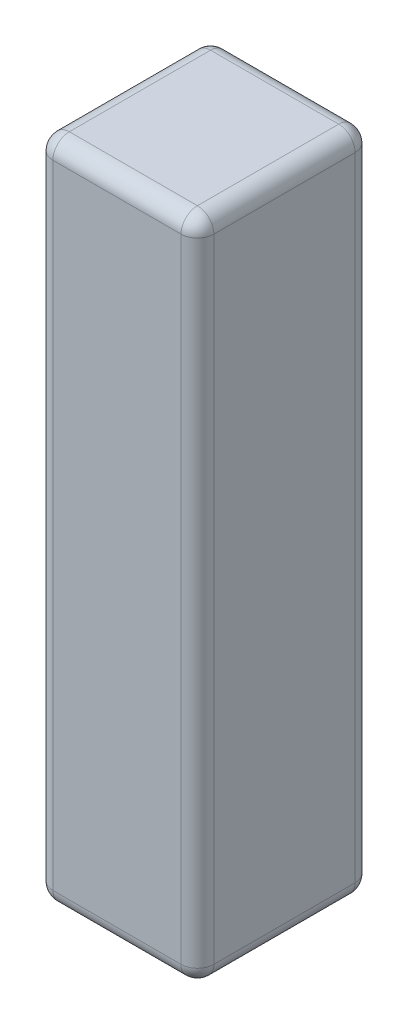
SolidWorks part; units mm, degrees
ref_plane "Front Plane" through (0, 0, 0) normal (0, 0, 1) x (1, 0, 0)
ref_plane "Top Plane" through (0, 0, 0) normal (0, 1, 0) x (1, 0, 0)
ref_plane "Right Plane" through (0, 0, 0) normal (1, 0, 0) x (0, 0, -1)
sketch "Sketch1" plane through (0, 0, 0) normal (0, 1, 0) x (1, 0, 0)
  line L1 (12.446, 13.462) -> (-12.446, 13.462)
  line L2 (12.446, 13.462) -> (12.446, -13.462)
  line L3 (12.446, -13.462) -> (-12.446, -13.462)
  line L4 (-12.446, 13.462) -> (-12.446, -13.462)
  line L5 (12.446, 13.462) -> (-12.446, -13.462) construction
  line L6 (12.446, -13.462) -> (-12.446, 13.462) construction
  point P0 (0, 0)
  dimension "D1" = 24.892
  dimension "D2" = 26.924
extrude "Boss-Extrude1" add sketch "Sketch1" along normal blind 102.87
fillet "Fillet1" radius 2.54 12 edges at (-12.446, 51.435, -13.462) (12.446, 51.435, -13.462) (-12.446, 51.435, 13.462) (12.446, 51.435, 13.462) (0, 0, 13.462) (12.446, 0, 0) (0, 0, -13.462) (-12.446, 0, 0) (0, 102.87, -13.462) (12.446, 102.87, 0) (0, 102.87, 13.462) (-12.446, 102.87, 0)
